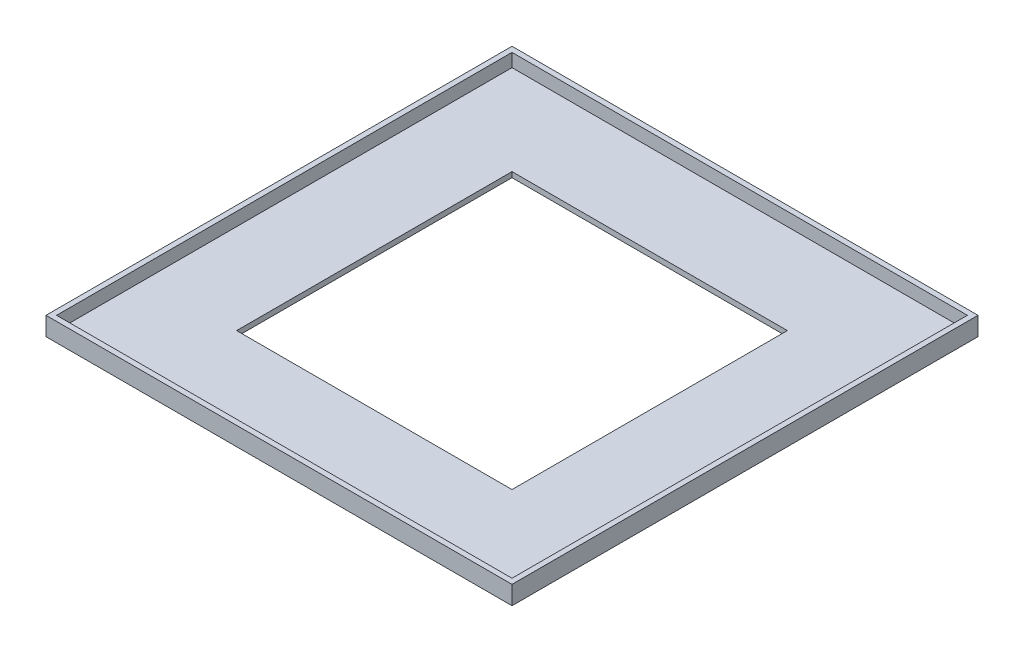
SolidWorks part; units mm, degrees
ref_plane "Front Plane" through (0, 0, 0) normal (0, 0, 1) x (1, 0, 0)
ref_plane "Top Plane" through (0, 0, 0) normal (0, 1, 0) x (1, 0, 0)
ref_plane "Right Plane" through (0, 0, 0) normal (1, 0, 0) x (0, 0, -1)
sketch "Sketch1" plane through (0, 0, 0) normal (0, 1, 0) x (1, 0, 0)
  line L1 (-44, 44) -> (44, 44)
  line L2 (-44, 44) -> (-44, -44)
  line L3 (-44, -44) -> (44, -44)
  line L4 (44, 44) -> (44, -44)
  line L5 (-44, 44) -> (44, -44) construction
  line L6 (-44, -44) -> (44, 44) construction
  point P0 (0, 0)
  dimension "D1" = 88
  dimension "D2" = 88
extrude "Boss-Extrude1" add sketch "Sketch1" along normal blind 3.5
sketch "Sketch2" plane through (0, 3.5, 0) normal (0, 1, 0) x (1, 0, 0)
  line L1 (-43, 43) -> (43, 43)
  line L2 (-43, 43) -> (-43, -43)
  line L3 (-43, -43) -> (43, -43)
  line L4 (43, 43) -> (43, -43)
  line L5 (-43, 43) -> (43, -43) construction
  line L6 (-43, -43) -> (43, 43) construction
  point P0 (0, 0)
  dimension "D1" = 86
  dimension "D2" = 86
extrude "Cut-Extrude1" cut sketch "Sketch2" against normal blind 2.5
sketch "Sketch3" plane through (0, 1, 0) normal (0, 1, 0) x (1, 0, 0)
  line L1 (-26, 26) -> (26, 26)
  line L2 (-26, 26) -> (-26, -26)
  line L3 (-26, -26) -> (26, -26)
  line L4 (26, 26) -> (26, -26)
  line L5 (-26, 26) -> (26, -26) construction
  line L6 (-26, -26) -> (26, 26) construction
  point P0 (0, 0)
  dimension "D1" = 52
  dimension "D2" = 52
extrude "Cut-Extrude2" cut sketch "Sketch3" against normal through all
